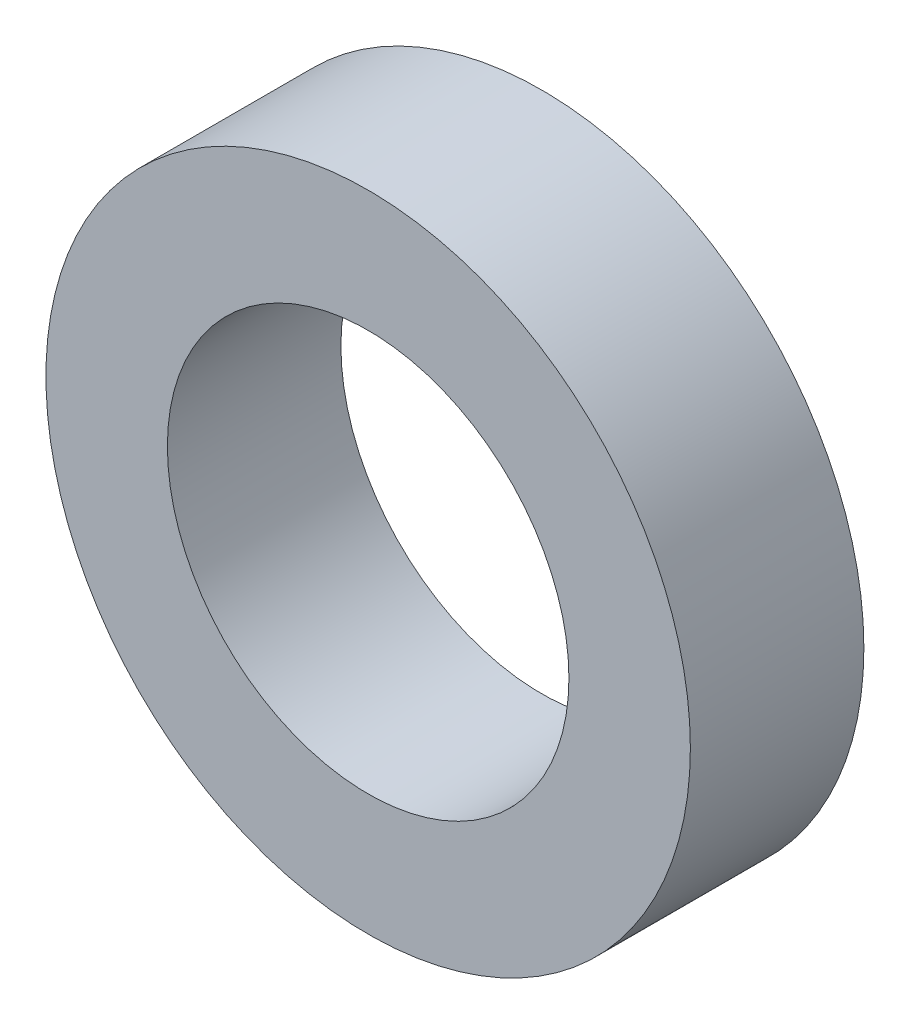
SolidWorks part; units mm, degrees
ref_plane "前视基准面" through (0, 0, 0) normal (0, 0, 1) x (1, 0, 0)
ref_plane "上视基准面" through (0, 0, 0) normal (0, 1, 0) x (1, 0, 0)
ref_plane "右视基准面" through (0, 0, 0) normal (1, 0, 0) x (0, 0, -1)
other "Configuration Table"
sketch "草图1" plane through (0, 0, 0) normal (0, 0, 1) x (1, 0, 0)
  circle A0 centre (0, 0) radius 13
  circle A1 centre (0, 0) radius 8.1
  dimension "D1" = 26
  dimension "D2" = 16.2
extrude "凸台-拉伸1" add sketch "草图1" along normal blind 7
